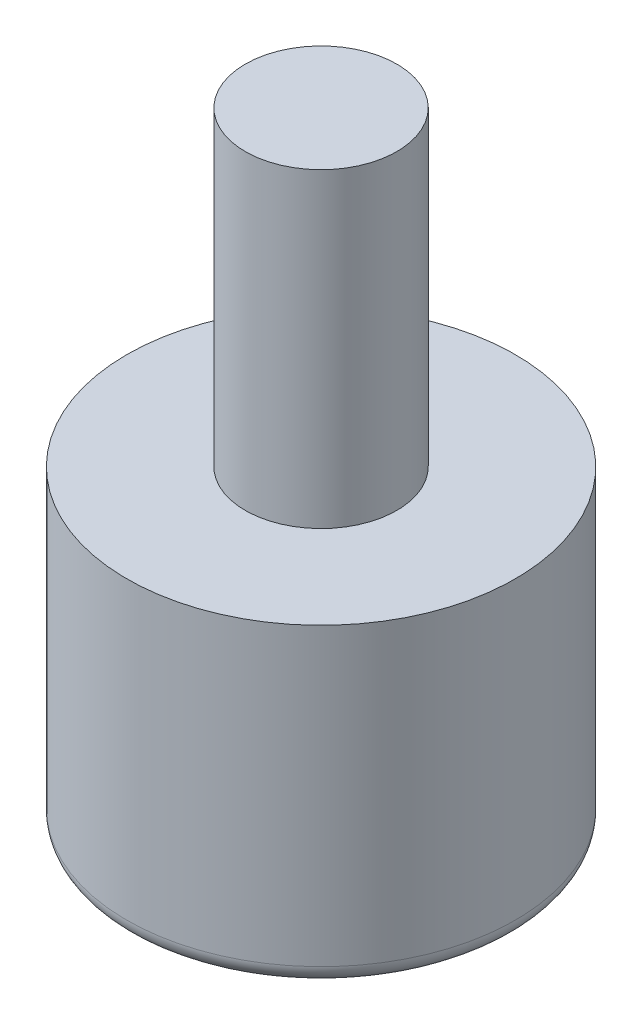
SolidWorks part; units mm, degrees
ref_plane "Plan de face" through (0, 0, 0) normal (0, 0, 1) x (1, 0, 0)
ref_plane "Plan de dessus" through (0, 0, 0) normal (0, 1, 0) x (1, 0, 0)
ref_plane "Plan de droite" through (0, 0, 0) normal (1, 0, 0) x (0, 0, -1)
sketch "Esquisse1" plane through (0, 0, 0) normal (0, 0, 1) x (1, 0, 0)
  line L0 (10.25, 0) -> (6, 0)
  line L1 (10.25, 0) -> (10.25, 16.6)
  line L2 (10.25, 16.6) -> (4, 16.6)
  line L3 (4, 16.6) -> (4, 33)
  line L4 (4, 33) -> (0, 33)
  line L5 (0, 33) -> (0, 0)
  line L6 (0, 0) -> (0, -3.4) construction
  line L7 (0, 0) -> (0, -3.4)
  arc A0 (6, 0) -> (0, -3.4) centre (0, 3.5941) cw
  dimension "D1" = 4
  dimension "D2" = 10.25
  dimension "D3" = 16.6
  dimension "D4" = 33
  dimension "D5" = 3.4
  dimension "D6" = 6
revolve "Révolution1" add sketch "Esquisse1" angle 360 about L5
fillet "Congé1" radius 1 1 edges at (-10.25, 0, 0)
